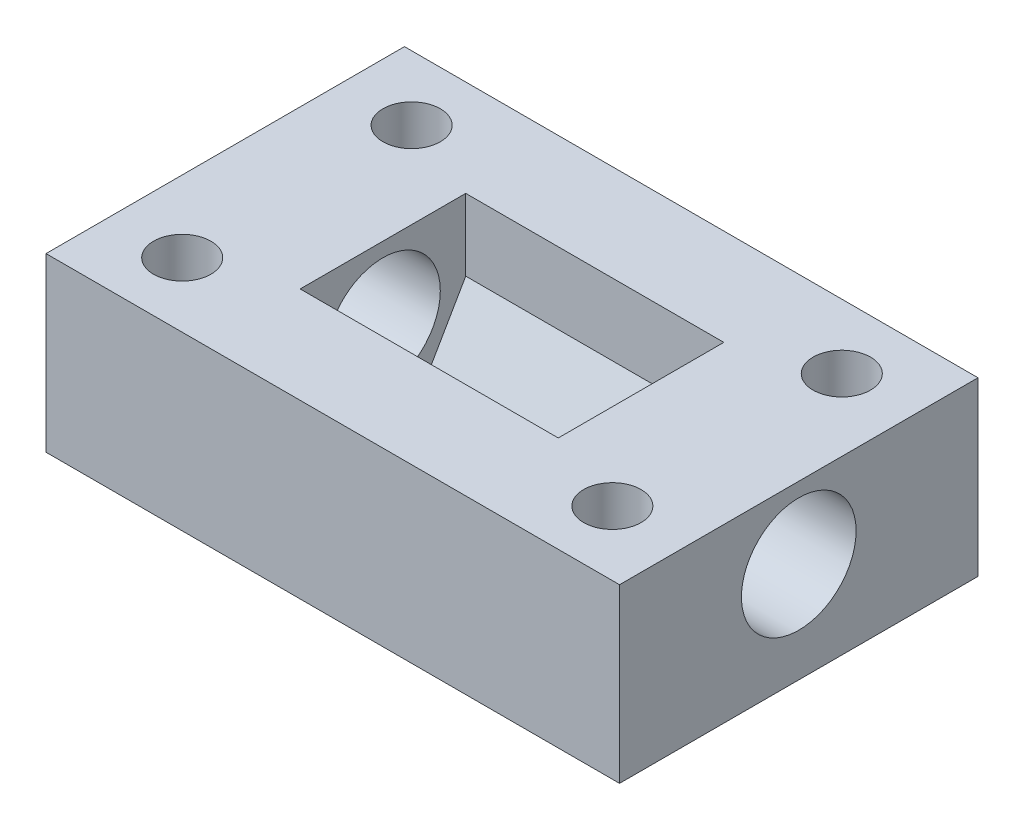
SolidWorks part; units mm, degrees
ref_plane "Front Plane" through (0, 0, 0) normal (0, 0, 1) x (1, 0, 0)
ref_plane "Top Plane" through (0, 0, 0) normal (0, 1, 0) x (1, 0, 0)
ref_plane "Right Plane" through (0, 0, 0) normal (1, 0, 0) x (0, 0, -1)
sketch "Sketch1" plane through (0, 0, 0) normal (0, 1, 0) x (1, 0, 0)
  line L1 (20, -12.5) -> (-20, -12.5)
  line L2 (20, -12.5) -> (20, 12.5)
  line L3 (20, 12.5) -> (-20, 12.5)
  line L4 (-20, -12.5) -> (-20, 12.5)
  line L5 (20, -12.5) -> (-20, 12.5) construction
  line L6 (20, 12.5) -> (-20, -12.5) construction
  point P0 (0, 0)
  dimension "D1" = 40
  dimension "D2" = 25
extrude "Boss-Extrude1" add sketch "Sketch1" along normal blind 12
sketch "Sketch2" plane through (0, 0, 0) normal (1, 0, 0) x (0, 0, -1)
  line L1 (-2.8868, 2) -> (2.8868, 2)
  line L2 (2.8868, 2) -> (5.7735, 7)
  line L6 (-5.7735, 7) -> (-2.8868, 2)
  line L7 (5.7735, 7) -> (3.0311, 11.75) [skipped]
  line L8 (-2.8868, 12) -> (-3.0311, 11.75) [skipped]
  line L9 (2.8868, 12) -> (-2.8868, 12) [skipped]
  line L10 (-5.7735, 7) -> (-5.7735, 12)
  line L11 (-12.5, 12) -> (12.5, 12) construction
  line L12 (5.7735, 7) -> (5.7735, 12)
  line L13 (5.7735, 12) -> (-5.7735, 12)
  dimension "D2" = 2
  dimension "D3" = 2.8868
extrude "Cut-Extrude1" cut sketch "Sketch2" against normal blind 9 and the other way blind 9
sketch "Sketch3" plane through (0, 0, 0) normal (1, 0, 0) x (0, 0, -1)
  line L0 (-12.5, 12) -> (12.5, 12) construction
  line L1 (-12.5, 12) -> (-12.5, 0) construction
  circle A0 centre (0, 7) radius 4
  dimension "D1" = 8
  dimension "D2" = 5
  dimension "D3" = 12.5
extrude "Cut-Extrude2" cut sketch "Sketch3" against normal through all both and the other way through all
sketch "Sketch4" plane through (0, 12, 0) normal (0, 1, 0) x (1, 0, 0)
  line L0 (0, -10.9943) -> (0, 11.1199) construction
  line L1 (16.6171, 0) -> (-17.8422, 0) construction
  circle A0 centre (-15, 8) radius 2
  circle A1 centre (15, 8) radius 2
  circle A2 centre (15, -8) radius 2
  circle A3 centre (-15, -8) radius 2
  dimension "D1" = 4
  dimension "D2" = 8
  dimension "D3" = 15
extrude "Cut-Extrude3" cut sketch "Sketch4" against normal through all both
